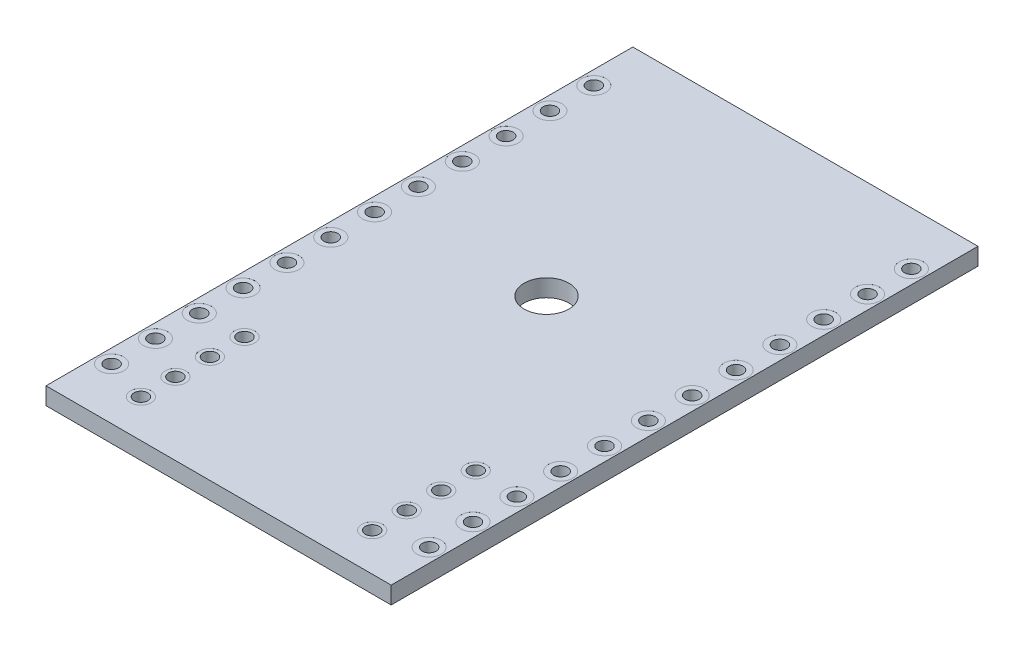
SolidWorks part; units mm, degrees
material "Power Circuit Board"
ref_plane "Front Plane" through (0, 0, 0) normal (0, 0, 1) x (1, 0, 0)
ref_plane "Top Plane" through (0, 0, 0) normal (0, 1, 0) x (1, 0, 0)
ref_plane "Right Plane" through (0, 0, 0) normal (1, 0, 0) x (0, 0, -1)
sketch "BaseS" plane through (0, 0, 0) normal (0, 1, 0) x (1, 0, 0)
  line L1 (-10, 17) -> (10, 17)
  line L2 (-10, 17) -> (-10, -17)
  line L3 (-10, -17) -> (10, -17)
  line L4 (10, 17) -> (10, -17)
  line L5 (-10, 17) -> (10, -17) construction
  line L6 (-10, -17) -> (10, 17) construction
  point P0 (0, 0)
  dimension "Width" = 20
  dimension "Length" = 34
extrude "Base" add sketch "BaseS" against normal mid plane 1
sketch "FasteningHoleS" plane through (0, 0.5, 0) normal (0, 1, 0) x (1, 0, 0)
  line L0 (0, 17) -> (0, 2) construction
  line L1 (10, 17) -> (-10, 17) construction
  circle A0 centre (0, 2) radius 1.3
  dimension "Diameter" = 2.6
  dimension "YDim" = 15
extrude "FasteningHole" cut sketch "FasteningHoleS" against normal through all
hole_wizard "Ø0.8 (0.8) Diameter Hole1" positions "Sketch2" profile "Sketch3" hole size "Ø0.8" standard "ANSI Metric" end condition through all
sketch "Sketch2" plane through (0, 0.5, 0) normal (0, 1, 0) x (1, 0, 0)
  line L0 (-10, 17) -> (-10, -17) construction
  line L1 (-10, -17) -> (10, -17) construction
  point P0 (-9.2, -14)
  dimension "XDim" = 0.8
  dimension "YDim" = 3
sketch "Sketch3" plane through (-9.2, 0.5, 14) normal (1, 0, 0) x (0, 0, 1)
  line L0 (0, 0) -> (0, 1)
  line L1 (0, 1) -> (0.4, 1)
  line L2 (0.4, 1) -> (0.4, 0)
  line L5 (0.4, 0) -> (0, 0)
  line L11 (0, -6.35) -> (0, 107.95) construction
  dimension "Thru Hole Dia." = 0.8
  dimension "Thru Hole Depth" = 1
sketch "SolderAccessCutS" plane through (0, 0.5, 0) normal (0, 1, 0) x (1, 0, 0)
  circle A3 centre (-9.2, -14) radius 0.7
  dimension "Dia" = 1.4
extrude "SolderAccessCut" cut sketch "SolderAccessCutS" against normal blind 0.001
mirror "SACVM" about plane through (0, 0, 0) normal (0, 1, 0) of "SolderAccessCut"
pattern_linear "HoleSACHorzLP" count 12 spacing 2.54 along (0, 0, -1) of "Ø0.8 (0.8) Diameter Hole1", "SolderAccessCut", "SACVM"
mirror "HSHM" about plane through (0, 0, 0) normal (1, 0, 0) of "HoleSACHorzLP", "Ø0.8 (0.8) Diameter Hole1", "SolderAccessCut", "SACVM"
sketch "GndPinS" plane through (0, 0.5, 0) normal (0, 1, 0) x (1, 0, 0)
  line L0 (-10, -17) -> (10, -17) construction
  circle A0 centre (6.7, -14.8) radius 0.4
  circle A1 centre (9.2, -14) radius 0.4 construction
  dimension "YDim" = 2.2
  dimension "XDim" = 2.5
extrude "GndPin" cut sketch "GndPinS" against normal through all
sketch "GPSACS" plane through (0, 0.5, 0) normal (0, 1, 0) x (1, 0, 0)
  circle A0 centre (6.7, -14.8) radius 0.6
  circle A1 centre (6.7, -14.8) radius 0.4 construction
  dimension "D1" = 0.2
extrude "GPSAC" cut sketch "GPSACS" against normal up to surface (0.001 mm away) up to face at (-9.2, 0.499, 14.7)
mirror "GPSACVM" about plane through (0, 0, 0) normal (0, 1, 0) of "GPSAC"
pattern_linear "GPLP" count 4 spacing 2 along (0, 0, -1) of "GndPin", "GPSAC", "GPSACVM"
mirror "GPHM" about plane through (0, 0, 0) normal (1, 0, 0) of "GPLP", "GPSACVM", "GPSAC", "GndPin"
sketch "ResistorS"
  line L2 (-5.25, -11.5) -> (5.25, -11.5) construction
  line L3 (0, -17) -> (0, -11.5) construction
  line L4 (-10, -17) -> (10, -17) construction
  line L5 (-7.5, -4) -> (-7.5, -2) construction
  line L7 (3, 0) -> (3, 2) construction
  line L8 (-10, 17) -> (-10, -17) construction
  line L9 (-3, 8) -> (-3, 7) construction
  point P0 (-7.5, -2)
  point P1 (7, -7)
  point P2 (5.25, -11.5)
  point P3 (-7.5, -4)
  point P4 (-6, -4.8)
  point P5 (-5.25, -11.5)
  point P6 (-3, 8)
  point P7 (-3, 7)
  point P8 (3, 2)
  point P9 (7, 5.4)
  point P10 (1.4, 4.5)
  point P14 (3, 0)
other "AlignGroup1" parameters "D1"=20, "D2"=34, "D3"=10.4642, "D4"=5.4459, "D5"=34, "D6"=11.8425, "D7"=4.8892, "D8"=1.3672, "D9"=1.3672, "D10"=1.9857, "D11"=15.8789, "D12"=34, "D13"=3.353, "D14"=20, "D15"=15, "D16"=0, "D17"=10, "D18"=17, "D19"=19, "D20"=12.2, "D21"=7, "D22"=24, "D23"=25, "D24"=21.5, "D25"=22.4, "D26"=30.1281
other "AlignGroup2"
other "AlignGroup3"
other "AlignGroup4"
sketch "VerticalResistorS" plane through (0, 0.5, 0) normal (0, 1, 0) x (1, 0, 0)
  point P0 (-5.25, -11.5)
  point P1 (5.25, -11.5)
  point P3 (-6, -4.8)
  point P5 (3, 0)
  point P7 (-7.5, -2)
  point P8 (-7.5, -4)
  point P10 (3, 2)
sketch "HorizontalResistorS" plane through (0, 0.5, 0) normal (0, 1, 0) x (1, 0, 0)
  point P0 (7, -7)
  point P1 (7, 5.4)
  point P3 (1.4, 4.5)
  point P5 (-3, 7)
  point P7 (-3, 8)
sketch "CapacitorS"
  line L0 (-6.2, 3.6) -> (-6.2, 2.2) construction
  line L1 (-3, 9) -> (-3, 6) construction
  line L2 (-3, 4) -> (-3, 5) construction
  line L3 (-3, 5) -> (-3, 6) construction
  line L4 (-4.5, -4) -> (-4.5, -5) construction
  line L5 (4, -7.5) -> (5, -7.5) construction
  line L6 (-3.8, 2) -> (-3.8, 2.8) construction
  line L7 (5.4, 12.5) -> (5.4, 11.5) construction
  line L8 (-10, -17) -> (10, -17) construction
  line L9 (-10, 17) -> (-10, -17) construction
  line L10 (1.5, 12) -> (2.5, 12) construction
  point P0 (-6.2, 3.6)
  point P1 (-6.2, 2.2)
  point P7 (5, -7.5)
  point P8 (-3, 9)
  point P9 (-3, 4)
  point P10 (-3, 5)
  point P13 (-4.5, -4)
  point P14 (-4.5, -5)
  point P15 (-5, -6.5)
  point P18 (4, -7.5)
  point P19 (2.5, -7.8)
  point P22 (-3.8, 2)
  point P23 (5.8, 10)
  point P24 (-3.8, 2.8)
  point P27 (5.4, 12.5)
  point P28 (5.4, 11.5)
  point P33 (2.5, 12)
  point P35 (1.5, 12)
  point P36 (1, 15)
  point P39 (0, 12.5)
  point P41 (2, 14.5)
  point P42 (3, 15)
other "AlignGroup5" parameters "D1"=0, "D2"=10.5, "D3"=12, "D4"=13, "D5"=19, "D6"=19.8, "D7"=19.2, "D8"=20.6, "D9"=21, "D10"=22, "D11"=0.7102, "D12"=26, "D13"=0, "D14"=9.2, "D15"=9.5, "D16"=27, "D17"=28.5, "D18"=29.5, "D19"=0, "D20"=5, "D21"=5.5, "D22"=12.5, "D23"=14, "D24"=15, "D25"=0, "D26"=3.8, "D27"=6.2, "D28"=7, "D29"=15.4, "D30"=15.8, "D31"=5.1629, "D32"=11.5, "D33"=12.5, "D34"=29, "D35"=32, "D36"=29.5, "D37"=10, "D38"=12, "D39"=31.5, "D40"=13, "D41"=32
other "AlignGroup6"
other "AlignGroup7"
other "AlignGroup8"
sketch "HorizontalCapacitorS" plane through (0, 0.5, 0) normal (0, 1, 0) x (1, 0, 0)
  point P0 (-5, -6.5)
  point P1 (-4.5, -5)
  point P3 (-4.5, -4)
  point P5 (2.5, -7.8)
  point P7 (-3.8, 2)
  point P9 (-3.8, 2.8)
  point P11 (-6.2, 2.2)
  point P13 (-6.2, 3.6)
  point P15 (5.8, 10)
  point P17 (-3, 5)
  point P18 (5.4, 11.5)
  point P19 (5.4, 12.5)
  point P20 (-3, 6)
  point P22 (-3, 9)
  point P24 (-3, 4)
  point P26 (2, 14.5)
  point P31 (0, 12.5)
sketch "VerticalCapacitorS" plane through (0, 0.5, 0) normal (0, 1, 0) x (1, 0, 0)
  point P0 (4, -7.5)
  point P1 (5, -7.5)
  point P3 (2.5, 12)
  point P5 (1.5, 12)
  point P7 (1, 15)
sketch "PushButtonS"
  line L0 (-10, -17) -> (10, -17) construction
  line L1 (-10, 17) -> (-10, -17) construction
  line L2 (0, 2) -> (0, -2) construction
  point P0 (0, -2)
  point P1 (-5.5, 7.5)
other "AlignGroup9" parameters "D1"=0, "D2"=15, "D3"=24.5, "D4"=0, "D5"=4.5
other "AlignGroup10"
sketch "LEDS" plane through (0, 0.5, 0) normal (0, 1, 0) x (1, 0, 0)
  line L0 (0, 2) -> (0, -5.5) construction
  line L2 (-10, -17) -> (10, -17) construction
  point P0 (0, -5.5)
other "AlignGroup11"
other "AlignGroup12" parameters "D1"=0, "D2"=11.5
sketch "TransistorS"
  line L0 (5.5, 3.5) -> (5.5, 0.5) construction
  line L1 (-10, -17) -> (10, -17) construction
  line L2 (-10, 17) -> (-10, -17) construction
  point P0 (5.5, 3.5)
  point P1 (5.5, 0.5)
other "AlignGroup13" parameters "D1"=0, "D2"=17.5, "D3"=20.5, "D4"=0, "D5"=15.5
other "AlignGroup14"
sketch "ICChipS"
  line L0 (-10, -17) -> (10, -17) construction
  line L1 (-10, 17) -> (-10, -17) construction
  point P0 (5.5, -3.5)
other "AlignGroup15" parameters "D1"=0, "D2"=13.5, "D3"=0, "D4"=15.5
other "AlignGroup16"
sketch "BuckRegulatorS"
  line L0 (-10, -17) -> (10, -17) construction
  line L1 (-10, 17) -> (-10, -17) construction
  point P0 (-5.5, -2.5)
other "AlignGroup17" parameters "D1"=0, "D2"=14.5, "D3"=34, "D4"=0, "D5"=4.5
other "AlignGroup18"
sketch "45DegreeCapacitorS" plane through (0, 0.5, 0) normal (0, 1, 0) x (1, 0, 0)
  point P0 (3, 15)
sketch "LargeSMDComponentS"
  line L0 (-10, 17) -> (-10, -17) construction
  line L1 (-10, -17) -> (10, -17) construction
  point P0 (-5.8, 0)
other "AlignGroup19" parameters "D1"=0, "D2"=4.2, "D3"=0, "D4"=17
other "AlignGroup20"
sketch "ResonatorS"
  line L1 (-10, 17) -> (-10, -17) construction
  line L2 (-10, -17) -> (10, -17) construction
  point P0 (6.5, 8)
other "AlignGroup21" parameters "D1"=34, "X1"=16.5, "D2"=0, "Y1"=25
other "AlignGroup22"
